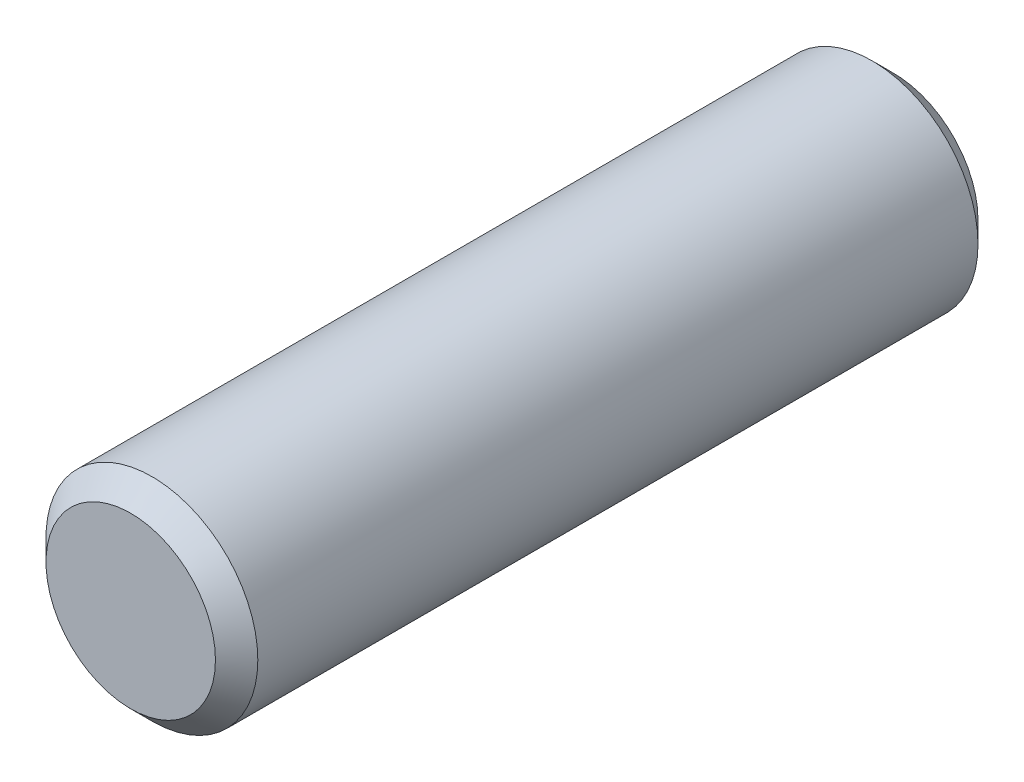
SolidWorks part; units mm, degrees
ref_plane "Front Plane" through (0, 0, 0) normal (0, 0, 1) x (1, 0, 0)
ref_plane "Top Plane" through (0, 0, 0) normal (0, 1, 0) x (1, 0, 0)
ref_plane "Right Plane" through (0, 0, 0) normal (1, 0, 0) x (0, 0, -1)
sketch "Sketch2" plane through (0, 0, 0) normal (0, 0, 1) x (1, 0, 0)
  circle A0 centre (0, 0) radius 5
  dimension "D1" = 10
extrude "Boss-Extrude1" add sketch "Sketch2" along normal blind 36
chamfer "Chamfer1" distance 1 angle 45 2 edges at (5, 0, 0) (5, 0, 36)
